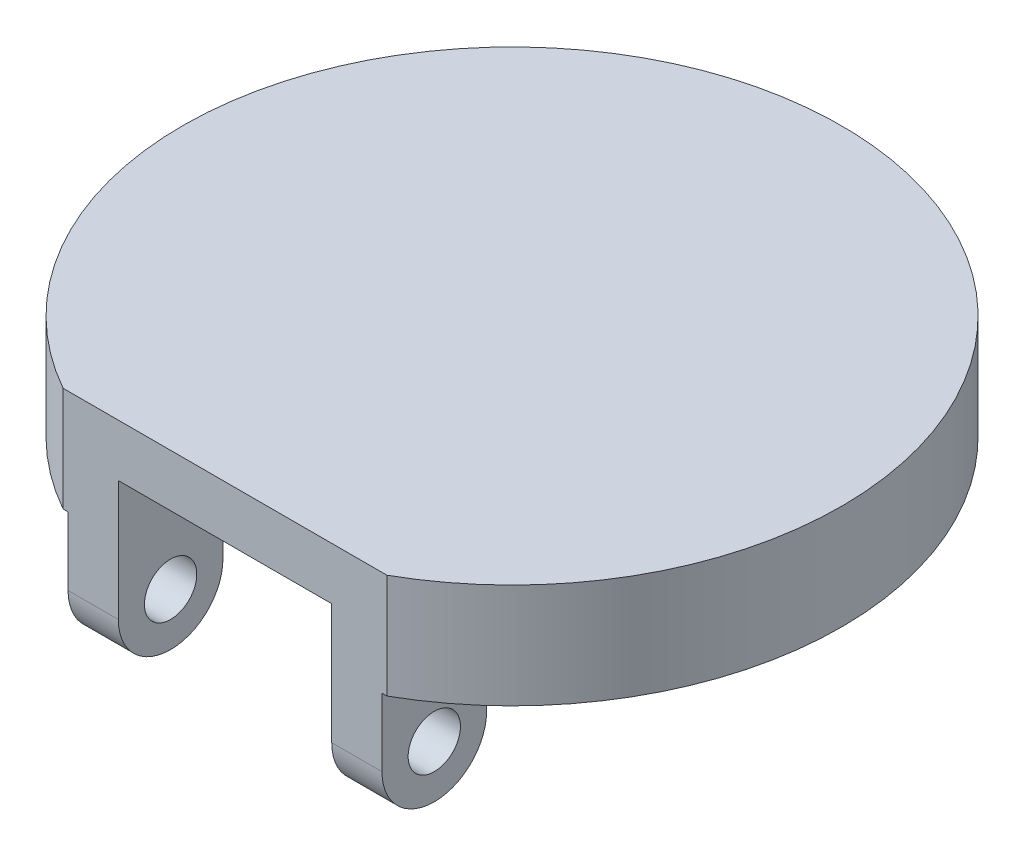
SolidWorks part; units mm, degrees
ref_plane "Front Plane" through (0, 0, 0) normal (0, 0, 1) x (1, 0, 0)
ref_plane "Top Plane" through (0, 0, 0) normal (0, 1, 0) x (1, 0, 0)
ref_plane "Right Plane" through (0, 0, 0) normal (1, 0, 0) x (0, 0, -1)
ref_plane "Plane1" through (6.35, 0, 0) normal (1, 0, 0) x (0, 0, -1)
sketch "Sketch1" plane through (0, 0, 0) normal (0, 1, 0) x (1, 0, 0)
  circle A0 centre (0, 0) radius 20
  dimension "D1" = 40
extrude "Boss-Extrude1" add sketch "Sketch1" along normal blind 6.35
sketch "Sketch2" plane through (6.35, 0, 0) normal (1, 0, 0) x (0, 0, -1)
  line L0 (-17.4201, 0) -> (-17.4201, -4.127)
  line L1 (-5.8492, 6.35) -> (-11.0701, 6.35)
  line L2 (-5.8492, 6.35) -> (-5.8492, 0)
  line L3 (-5.8492, 0) -> (-7.8951, 0)
  line L8 (-11.0701, -3.175) -> (-11.0701, -4.127)
  line L9 (-9.525, -0.254) -> (-18.9652, -0.254) construction
  line L11 (20, 6.35) -> (-20, 6.35) construction
  line L12 (-20, 0) -> (20, 0) construction
  arc A0 (-17.4201, -4.127) -> (-11.0701, -4.127) centre (-14.2451, -4.127) ccw
  arc A1 (-11.0701, 6.35) -> (-17.4201, 0) centre (-11.0701, 0) ccw
  arc A2 (-7.8951, 0) -> (-11.0701, -3.175) centre (-7.8951, -3.175) ccw
  circle A3 centre (-14.2451, -4.127) radius 1.5875 construction
  point P7 (-14.2451, -0.254)
  dimension "D2" = 6.35
  dimension "D3" = 3.175
  dimension "D1" = 6.35
extrude "Boss-Extrude2" add sketch "Sketch2" along normal blind 3.175
mirror "Mirror1" about plane through (0, 0, 0) normal (1, 0, 0) of "Boss-Extrude2"
sketch "Sketch3" plane through (9.525, 0, 0) normal (1, 0, 0) x (0, 0, -1)
  circle A0 centre (-14.2451, -4.127) radius 1.5875
  arc A1 (-17.4201, -4.127) -> (-11.0701, -4.127) centre (-14.2451, -4.127) ccw construction
  dimension "D1" = 3.175
extrude "Cut-Extrude1" cut sketch "Sketch3" against normal through all
sketch "Sketch5" plane through (0, 0, 0) normal (0, -1, 0) x (1, 0, 0)
  line L0 (6.35, 17.4201) -> (6.35, 7.8951) construction
  line L1 (-6.35, 7.8951) -> (-6.35, 17.4201) construction
  line L2 (6.35, 18.9652) -> (6.35, 7.6056)
  line L3 (-6.35, 7.6056) -> (-6.35, 18.9652)
  arc A0 (-6.35, 7.6056) -> (6.35, 7.6056) centre (0, 0) ccw
  circle A1 centre (0, 0) radius 20 construction
  arc A2 (6.35, 18.9652) -> (-6.35, 18.9652) centre (0, 0) ccw
extrude "Cut-Extrude2" cut sketch "Sketch5" against normal blind 3.175
sketch "Sketch6" plane through (6.35, 0, 0) normal (1, 0, 0) x (0, 0, -1)
  line L1 (-17.4201, 0) -> (-26.4896, 0)
  line L2 (-17.4201, 0) -> (-17.4201, 11.7552)
  line L3 (-17.4201, 11.7552) -> (-26.4896, 11.7552)
  line L4 (-26.4896, 0) -> (-26.4896, 11.7552)
extrude "Cut-Extrude3" cut sketch "Sketch6" against normal through all both and the other way through all
sketch "Sketch7" plane through (0, 0, 0) normal (1, 0, 0) x (0, 0, -1)
  line L1 (-6.6469, 0) -> (-6.6469, 3.175)
  line L2 (-6.6469, 3.175) -> (-7.6056, 3.175)
  line L5 (-7.6056, 3.175) -> (-17.4201, 3.175)
  line L6 (-17.4201, 3.175) -> (-17.4201, -4.127)
  line L7 (-11.0701, -4.127) -> (-11.0701, -3.175)
  line L8 (-7.8951, 0) -> (-7.6056, 0)
  line L9 (-7.6056, 0) -> (-7.6056, 3.175)
  line L10 (-7.6056, 3.175) -> (-17.4201, 3.175)
  line L11 (-17.4201, 3.175) -> (-17.4201, -4.127)
  line L12 (-11.0701, -4.127) -> (-11.0701, -3.175)
  line L13 (-7.8951, 0) -> (-6.6469, 0)
  arc A2 (-17.4201, -4.127) -> (-11.0701, -4.127) centre (-14.2451, -4.127) ccw
  arc A3 (-7.8951, 0) -> (-11.0701, -3.175) centre (-7.8951, -3.175) ccw
  arc A4 (-17.4201, -4.127) -> (-11.0701, -4.127) centre (-14.2451, -4.127) ccw
  arc A5 (-7.8951, 0) -> (-11.0701, -3.175) centre (-7.8951, -3.175) ccw
  dimension "D1" = 0
extrude "Cut-Extrude4" cut sketch "Sketch7" against normal offset from surface 0.127 and the other way offset from surface (6.477 mm away) 0.127 other way up to face at (6.35, -4.127, 12.6576)
